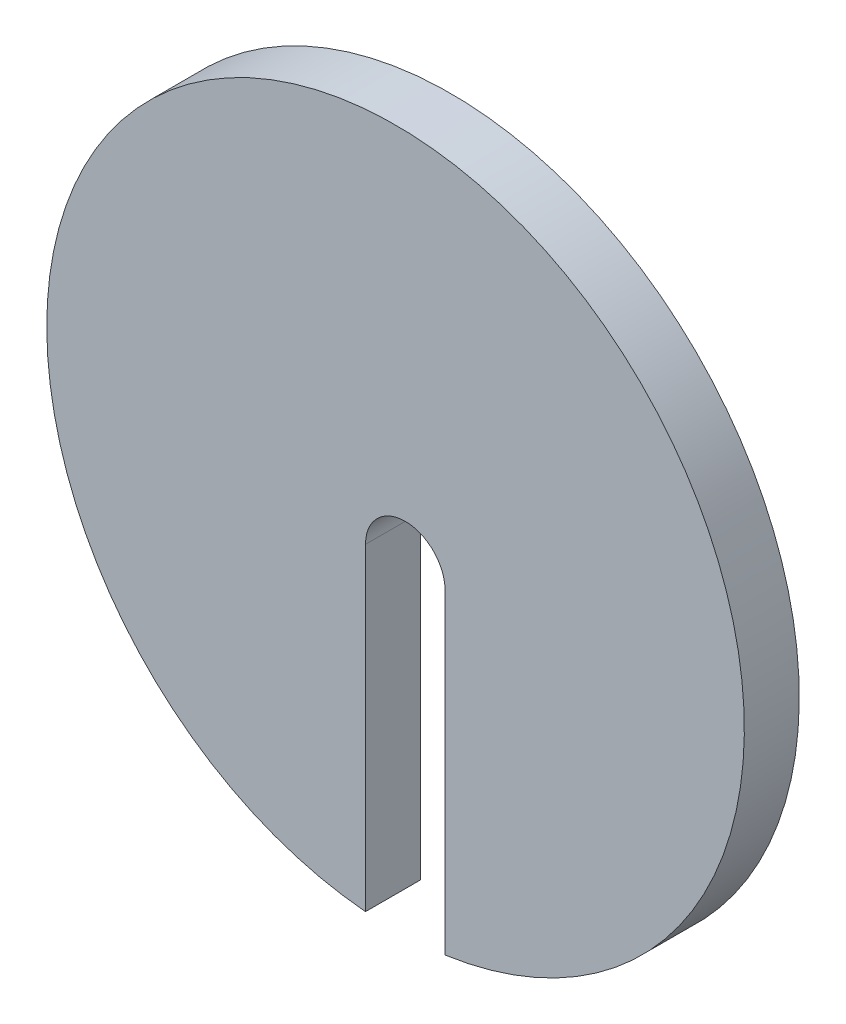
SolidWorks part; units mm, degrees
ref_plane "Front Plane" through (0, 0, 0) normal (0, 0, 1) x (1, 0, 0)
ref_plane "Top Plane" through (0, 0, 0) normal (0, 1, 0) x (1, 0, 0)
ref_plane "Right Plane" through (0, 0, 0) normal (1, 0, 0) x (0, 0, -1)
sketch "Sketch1" plane through (0, 0, 0) normal (0, 0, 1) x (1, 0, 0)
  circle A0 centre (0, 0) radius 63.5
  dimension "D1" = 127
extrude "Boss-Extrude1" add sketch "Sketch1" along normal blind 10
sketch "Sketch2" plane through (0, 0, 10) normal (0, 0, 1) x (1, 0, 0)
  line L0 (-5.4694, -63.264) -> (-5.4694, -5.3426)
  line L1 (9.0167, -5.3426) -> (9.0167, -62.8566)
  arc A0 (-5.4694, -5.3426) -> (9.0167, -5.3426) centre (1.7737, -5.3426) cw
  arc A1 (9.0167, -62.8566) -> (-5.4694, -63.264) centre (1.7679, -62.8566) cw
extrude "Cut-Extrude1" cut sketch "Sketch2" against normal blind 10
